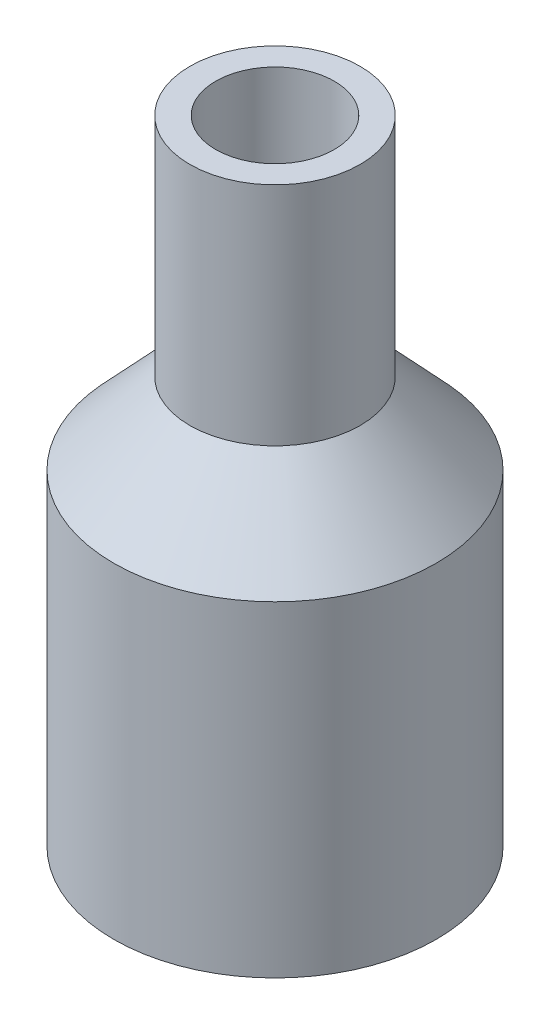
SolidWorks part; units mm, degrees
ref_plane "Plan de face" through (0, 0, 0) normal (0, 0, 1) x (1, 0, 0)
ref_plane "Plan de dessus" through (0, 0, 0) normal (0, 1, 0) x (1, 0, 0)
ref_plane "Plan de droite" through (0, 0, 0) normal (1, 0, 0) x (0, 0, -1)
sketch "Esquisse1" plane through (0, 0, 0) normal (0, 0, 1) x (1, 0, 0)
  line L0 (0, 0) -> (0, 53.316)
  line L1 (0, 53.316) -> (12.4629, 66.5946)
  line L2 (12.4629, 66.5946) -> (12.4629, 103.5978)
  line L3 (12.4629, 103.5978) -> (16.6871, 103.5978)
  line L4 (16.6871, 103.5978) -> (16.6871, 65.8174)
  line L5 (16.6871, 65.8174) -> (3.7179, 51.9994)
  line L6 (3.7179, 51.9994) -> (3.7179, 0)
  line L7 (3.7179, 0) -> (0, 0)
  line L8 (0, 0) -> (0.2446, -0.3594)
  line L9 (26.3895, 105.8029) -> (26.3895, -50.5385) construction
revolve "Révolution1" add sketch "Esquisse1" angle 360 about L9
